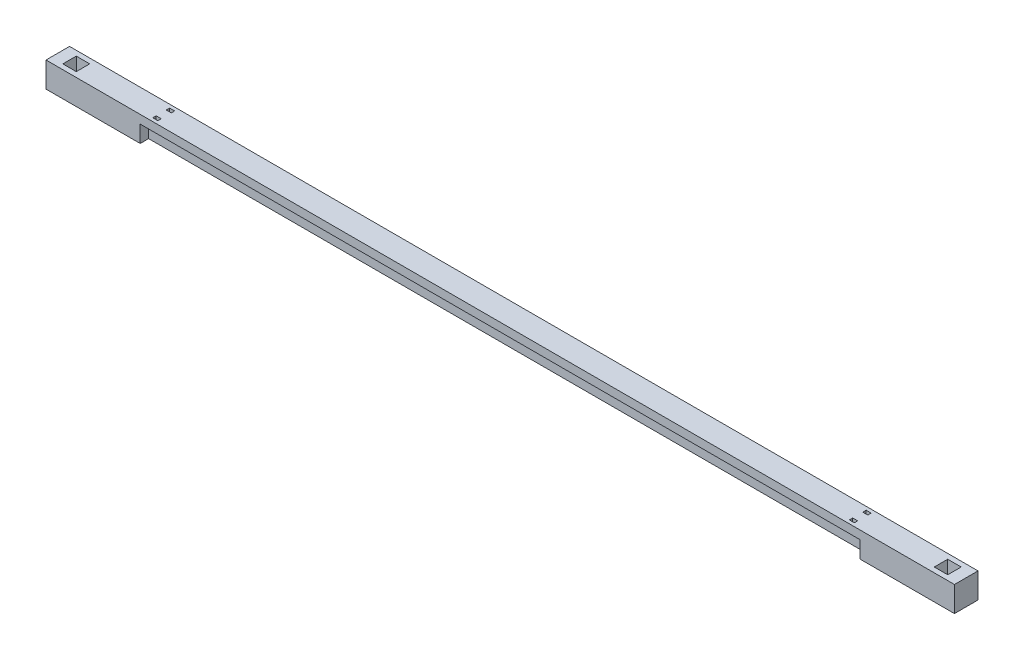
SolidWorks part; units mm, degrees
material "松木"
ref_plane "前视基准面" through (0, 0, 0) normal (0, 0, 1) x (1, 0, 0)
ref_plane "上视基准面" through (0, 0, 0) normal (0, 1, 0) x (1, 0, 0)
ref_plane "右视基准面" through (0, 0, 0) normal (1, 0, 0) x (0, 0, -1)
sketch "草图1" plane through (0, 0, 0) normal (0, 1, 0) x (1, 0, 0)
  line L1 (0, 0) -> (5400, 0)
  line L2 (0, 0) -> (0, 40)
  line L3 (0, 40) -> (5400, 40)
  line L4 (5400, 0) -> (5400, 40)
  dimension "D1" = 5400
  dimension "D2" = 40
extrude "凸台-拉伸1" add sketch "草图1" along normal blind 100
sketch "草图2" plane through (0, 100, 0) normal (0, 1, 0) x (1, 0, 0)
  line L0 (0, 40) -> (0, 0) construction
  line L1 (0, -50) -> (5400, -50)
  line L2 (0, -50) -> (0, 90)
  line L3 (0, 90) -> (5400, 90)
  line L4 (5400, -50) -> (5400, 90)
  point P4 (0, 20)
  point P7 (0, 20)
  dimension "D1" = 5400
  dimension "D2" = 140
extrude "凸台-拉伸2" add sketch "草图2" along normal blind 50
sketch "草图3" plane through (0, 100, 0) normal (0, -1, 0) x (1, 0, 0)
  line L0 (560, 50) -> (4840, 50)
  line L1 (0, 50) -> (5400, 50) construction
  line L2 (615, -50) -> (615, -70)
  line L3 (615, 10) -> (645, 10)
  line L4 (615, 10) -> (615, 30)
  line L5 (615, 30) -> (645, 30)
  line L6 (645, 10) -> (645, 30)
  line L7 (615, -70) -> (645, -70)
  line L8 (645, -70) -> (645, -50)
  line L9 (645, -50) -> (615, -50)
  line L10 (5400, -90) -> (0, -90) construction
  dimension "D1" = 4280
  dimension "D2" = 560
  dimension "D3" = 30
  dimension "D4" = 20
  dimension "D5" = 20
  dimension "D6" = 55
  dimension "D7" = 20
  dimension "D8" = 20
  dimension "D9" = 30
extrude "切除-拉伸1" cut sketch "草图3" against normal through all contours L8 L9 L2 L7 | L3 L6 L5 L4
pattern_linear "阵列(线性)1" count 2 spacing 4140 along (1, 0, 0) of "切除-拉伸1"
sketch "草图4" plane through (0, 0, 0) normal (0, -1, 0) x (1, 0, 0)
  line L1 (5400, -90) -> (4840, -90)
  line L2 (5400, -90) -> (5400, 50)
  line L3 (5400, 50) -> (4840, 50)
  line L4 (4840, -90) -> (4840, 50)
  dimension "D1" = 140
  dimension "D2" = 560
extrude "凸台-拉伸3" add sketch "草图4" against normal blind 100
pattern_linear "阵列(线性)2" count 2 spacing 4840 along (-1, 0, 0) of "凸台-拉伸3"
sketch "草图5" plane through (0, 150, 0) normal (0, 1, 0) x (1, 0, 0)
  line L0 (5400, -50) -> (5400, 90) construction
  line L1 (5330, 60) -> (5250, 60)
  line L2 (5330, 60) -> (5330, -20)
  line L3 (5330, -20) -> (5250, -20)
  line L4 (5250, 60) -> (5250, -20)
  line L5 (0, -50) -> (5400, -50) construction
  point P6 (5400, 20)
  dimension "D1" = 80
  dimension "D2" = 80
  dimension "D3" = 70
  dimension "D4" = 30
extrude "切除-拉伸2" cut sketch "草图5" against normal blind 100
ref_plane "基准面1" through (2700, 0, 0) normal (1, 0, 0) x (0, 0, -1)
mirror "镜向1" about plane through (2700, 0, 0) normal (1, 0, 0) of "切除-拉伸2"
